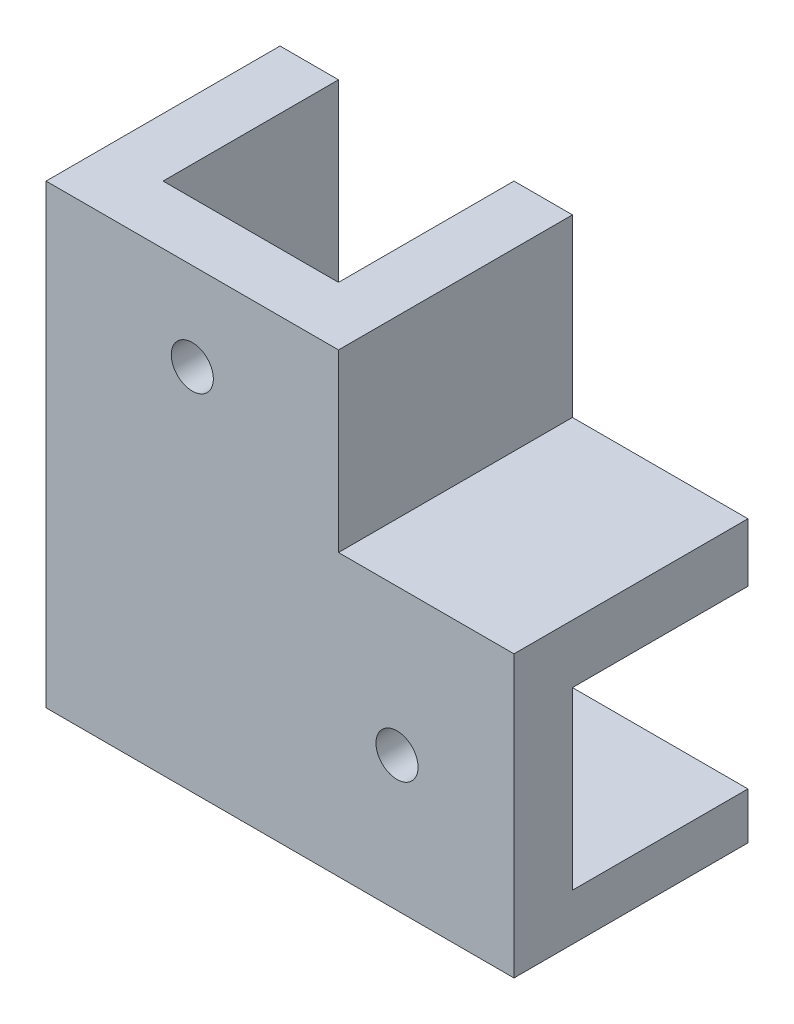
SolidWorks part; units mm, degrees
ref_plane "前视基准面" through (0, 0, 0) normal (0, 0, 1) x (1, 0, 0)
ref_plane "上视基准面" through (0, 0, 0) normal (0, 1, 0) x (1, 0, 0)
ref_plane "右视基准面" through (0, 0, 0) normal (1, 0, 0) x (0, 0, -1)
sketch "Sketch1" plane through (0, 0, 0) normal (0, 0, 1) x (1, 0, 0)
  line L0 (-7.5299, -25.8068) -> (27.4701, -25.8068)
  line L3 (-7.5299, 9.1932) -> (7.4701, 9.1932)
  line L4 (-7.5299, 9.1932) -> (-7.5299, -25.8068)
  line L6 (7.4701, 9.1932) -> (7.4701, -10.8068)
  line L7 (27.4701, -25.8068) -> (27.4701, -10.8068)
  line L8 (27.4701, -10.8068) -> (7.4701, -10.8068)
  dimension "D1" = 15
  dimension "D2" = 35
  dimension "D3" = 35
  dimension "D4" = 15
extrude "Boss-Extrude1" add sketch "Sketch1" along normal blind 5
sketch "Sketch2" plane through (0, 0, 0) normal (0, 0, -1) x (-1, 0, 0)
  line L0 (-7.4701, 9.1932) -> (-12.4701, 9.1932)
  line L1 (-12.4701, 9.1932) -> (-12.4701, -5.8068)
  line L2 (-12.4701, -5.8068) -> (-27.4701, -5.8068)
  line L3 (-27.4701, -10.8068) -> (-27.4701, -5.8068)
  line L4 (-27.4701, -10.8068) -> (-7.4701, -10.8068)
  line L5 (-7.4701, -10.8068) -> (-7.4701, 9.1932)
  dimension "D1" = 5
  dimension "D2" = 5
extrude "Boss-Extrude2" add sketch "Sketch2" along normal blind 15 separate body
sketch "Sketch3" plane through (0, 0, 0) normal (0, 0, -1) x (-1, 0, 0)
  line L0 (7.5299, 9.1932) -> (12.5299, 9.1932)
  line L1 (7.5299, -25.8068) -> (12.5299, -25.8068)
  line L2 (12.5299, -25.8068) -> (12.5299, 9.1932)
  line L3 (7.5299, -25.8068) -> (7.5299, 9.1932)
  dimension "D1" = 5
extrude "Boss-Extrude3" add sketch "Sketch3" along normal blind 15 separate body
sketch "Sketch4" plane through (0, 0, 0) normal (0, 0, 1) x (1, 0, 0)
  line L1 (-12.5299, 9.1932) -> (-7.5299, 9.1932)
  line L2 (-12.5299, 9.1932) -> (-12.5299, -25.8068)
  line L3 (-12.5299, -25.8068) -> (-7.5299, -25.8068)
  line L4 (-7.5299, 9.1932) -> (-7.5299, -25.8068)
extrude "Boss-Extrude4" add sketch "Sketch4" along normal blind 5
sketch "Sketch5" plane through (0, 0, 0) normal (0, 0, 1) x (1, 0, 0)
  line L0 (7.4701, 9.1932) -> (7.4701, -10.8068)
  line L1 (7.4701, -10.8068) -> (27.4701, -10.8068)
  line L2 (27.4701, -10.8068) -> (27.4701, -5.8068)
  line L3 (27.4701, -5.8068) -> (12.4701, -5.8068)
  line L4 (12.4701, -5.8068) -> (12.4701, 9.1932)
  line L5 (12.4701, 9.1932) -> (7.4701, 9.1932)
extrude "Boss-Extrude5" add sketch "Sketch5" along normal blind 5
sketch "Sketch7" plane through (0, 0, 0) normal (0, 0, -1) x (-1, 0, 0)
  line L0 (-27.4701, -25.8068) -> (-27.4701, -10.8068) construction
  line L1 (-27.4701, -10.8068) -> (-7.4701, -10.8068) construction
  line L2 (-7.4701, 9.1932) -> (7.5299, 9.1932) construction
  line L3 (7.5299, 9.1932) -> (7.5299, -25.8068) construction
  circle A0 centre (0.0299, 1.6932) radius 1.8
  circle A1 centre (-17.4701, -18.3068) radius 1.8
  dimension "D1" = 3.6
  dimension "D2" = 3.6
  dimension "D3" = 10
  dimension "D5" = 7.5
  dimension "D6" = 7.5
  dimension "D4" = 7.5
extrude "Cut-Extrude1" cut sketch "Sketch7" against normal through all
sketch "Sketch8" plane through (0, 0, -15) normal (0, 0, -1) x (-1, 0, 0)
  line L0 (12.5299, 9.1932) -> (-12.4701, 9.1932)
  line L1 (-12.4701, 9.1932) -> (-12.4701, -5.8068)
  line L2 (-12.4701, -5.8068) -> (-27.4701, -5.8068)
  line L3 (-27.4701, -5.8068) -> (-27.4701, -10.8068) construction
  line L4 (-27.4701, -5.8068) -> (-27.4701, -25.8068)
  line L5 (-27.4701, -25.8068) -> (12.5299, -25.8068)
  line L6 (12.5299, -25.8068) -> (12.5299, 9.1932)
sketch "Sketch9" plane through (0, 0, -15) normal (0, 0, -1) x (-1, 0, 0)
  line L0 (12.5299, -10.8068) -> (7.5299, -10.8068)
  line L2 (7.5299, -10.8068) -> (7.5299, -25.8068)
  line L3 (7.5299, -25.8068) -> (12.5299, -25.8068)
  line L4 (12.5299, -10.8068) -> (12.5299, -25.8068)
  dimension "D1" = 15
extrude "Boss-Extrude6" add sketch "Sketch9" along normal blind 13
sketch "Sketch10" plane through (0, -25.8068, 0) normal (0, -1, 0) x (1, 0, 0)
  line L0 (-7.5299, -28) -> (-7.5299, 0) construction
  line L1 (-7.5299, 0) -> (7.4701, 0)
  line L2 (-7.5299, 0) -> (-7.5299, -25)
  line L3 (-7.5299, -25) -> (7.4701, -25)
  line L4 (7.4701, 0) -> (7.4701, -25)
  dimension "D1" = 15
sketch "Sketch12" plane through (0, -25.8068, 0) normal (0, -1, 0) x (1, 0, 0)
  line L5 (7.4701, -28) -> (-12.5299, -28)
  line L6 (7.4701, -28) -> (7.4701, -15)
  line L7 (7.4701, 5) -> (-12.5299, 5)
  line L8 (-12.5299, -28) -> (-12.5299, 5)
  line L9 (27.4701, 5) -> (7.4701, 5)
  line L10 (27.4701, 5) -> (27.4701, -15)
  line L11 (27.4701, -15) -> (7.4701, -15)
  line L12 (-7.5299, -28) -> (-12.5299, -28) construction
  dimension "D1" = 0
extrude "Boss-Extrude7" add sketch "Sketch12" along normal blind 4
sketch "Sketch13" plane through (0, -29.8068, 0) normal (0, -1, 0) x (1, 0, 0)
  line L1 (7.4701, 0) -> (7.4701, -25) construction
  line L2 (-12.5299, -28) -> (7.4701, -28) construction
  circle A0 centre (-0.0299, -20.5) radius 1.5
  dimension "D1" = 3
  dimension "D2" = 7.5
  dimension "D3" = 7.5
extrude "Cut-Extrude4" cut sketch "Sketch13" against normal through all
